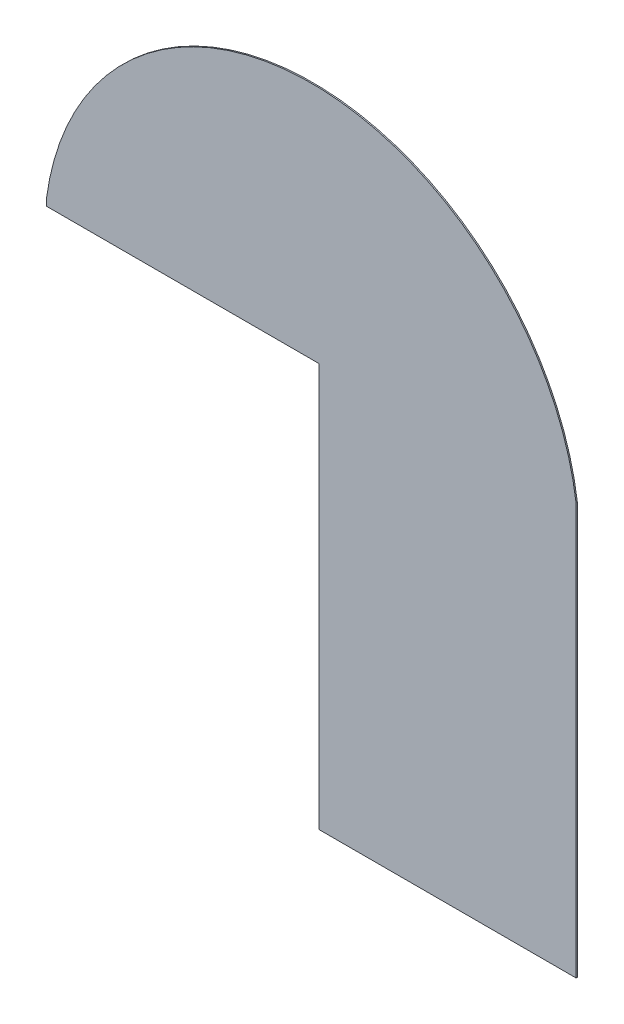
SolidWorks part; units mm, degrees
ref_plane "Front Plane" through (0, 0, 0) normal (0, 0, 1) x (1, 0, 0)
ref_plane "Top Plane" through (0, 0, 0) normal (0, 1, 0) x (1, 0, 0)
ref_plane "Right Plane" through (0, 0, 0) normal (1, 0, 0) x (0, 0, -1)
sketch "Sketch1" plane through (0, 0, 0) normal (0, 0, 1) x (1, 0, 0)
  line L2 (1030, 800) -> (1030, -800)
  line L3 (1030, -800) -> (-1030, -800)
  line L4 (-1030, 800) -> (-1030, -800)
  line L5 (1030, 800) -> (-1030, -800) construction
  line L6 (1030, -800) -> (-1030, 800) construction
  arc A1 (-1030, 800) -> (1030, 800) centre (0, 660.6111) cw
  point P0 (0, 0)
  point P1 (0, 0)
  point P10 (0, 1700)
  dimension "D1" = 2060
  dimension "D2" = 900
  dimension "D3" = 1600
extrude "Boss-Extrude1" add sketch "Sketch1" along normal mid plane 5
sketch "Sketch2" plane through (0, 0, 2.5) normal (0, 0, 1) x (1, 0, 0)
  line L0 (-1030, 800) -> (30, 800)
  line L1 (30, 800) -> (30, -800)
  line L2 (-1030, -800) -> (1030, -800) construction
  line L3 (-1030, 800) -> (-1030, -800)
  line L4 (-1030, -800) -> (1030, -800)
  line L5 (1030, -800) -> (1030, 800)
  line L6 (-1030, 800) -> (-1030, -800)
  line L7 (-1030, -800) -> (1030, -800)
  line L8 (1030, -800) -> (1030, 800) construction
  line L9 (-1030, 770) -> (30, 770)
  arc A1 (1030, 800) -> (-1030, 800) centre (0, 660.6111) ccw
  arc A2 (1030, 800) -> (-1030, 800) centre (0, 660.6111) ccw construction
  line M8 (-1030, -800) -> (1030, -800)
  dimension "D2" = 1060
  dimension "D3" = 30
  dimension "D1" = 0
extrude "Cut-Extrude2" cut sketch "Sketch2" against normal through all contours L9 L6 L1 M8
